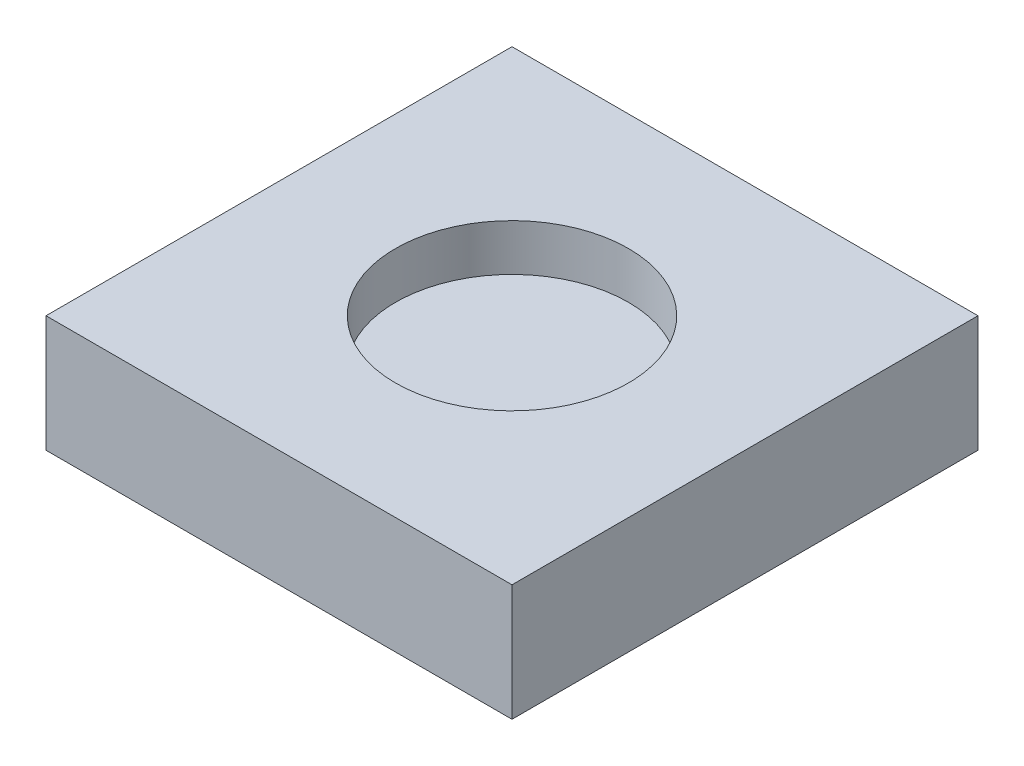
SolidWorks part; units mm, degrees
ref_plane "Front Plane" through (0, 0, 0) normal (0, 0, 1) x (1, 0, 0)
ref_plane "Top Plane" through (0, 0, 0) normal (0, 1, 0) x (1, 0, 0)
ref_plane "Right Plane" through (0, 0, 0) normal (1, 0, 0) x (0, 0, -1)
sketch "Sketch1" plane through (0, 0, 0) normal (0, 1, 0) x (1, 0, 0)
  line L1 (-10, -10) -> (10, -10)
  line L2 (-10, -10) -> (-10, 10)
  line L3 (-10, 10) -> (10, 10)
  line L4 (10, -10) -> (10, 10)
  line L5 (-10, -10) -> (10, 10) construction
  line L6 (-10, 10) -> (10, -10) construction
  point P0 (0, 0)
  dimension "D1" = 20
  dimension "D2" = 20
extrude "Boss-Extrude1" add sketch "Sketch1" along normal blind 5
sketch "Sketch2" plane through (0, 5, 0) normal (0, 1, 0) x (1, 0, 0)
  circle A0 centre (0, 0) radius 5
  dimension "D1" = 10
extrude "Cut-Extrude1" cut sketch "Sketch2" against normal blind 2
sketch "Sketch3" plane through (0, 0, 0) normal (0, -1, 0) x (1, 0, 0)
  circle A0 centre (0, 0) radius 1
  dimension "D1" = 2
extrude "Cut-Extrude2" cut sketch "Sketch3" against normal blind 2
fillet "Fillet1" radius 1 1 edges at (0, 2, -1)
